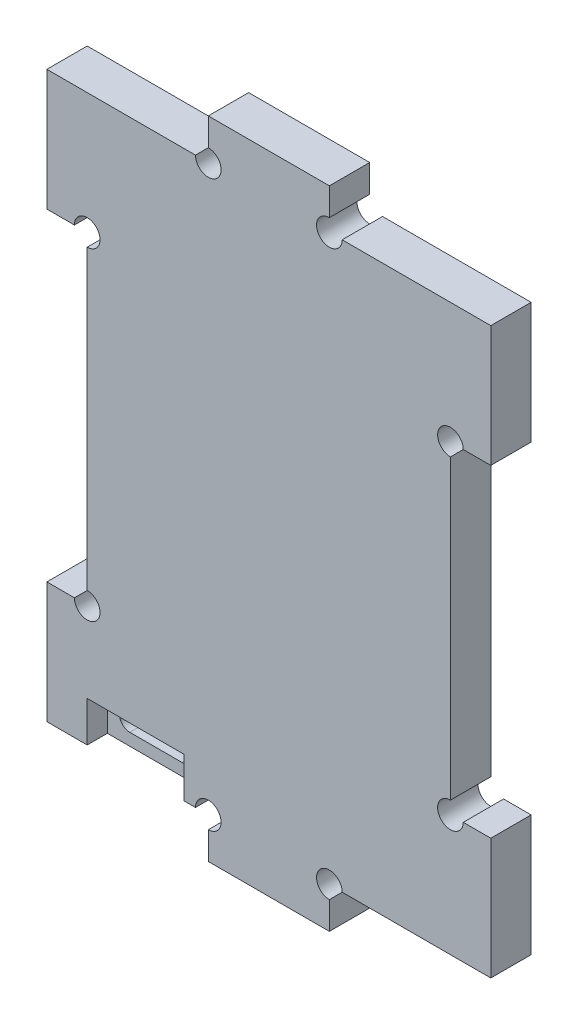
SolidWorks part; units mm, degrees
material "Acrylic (Medium-high impact)"
ref_plane "Front Plane" through (0, 0, 0) normal (0, 0, 1) x (1, 0, 0)
ref_plane "Top Plane" through (0, 0, 0) normal (0, 1, 0) x (1, 0, 0)
ref_plane "Right Plane" through (0, 0, 0) normal (1, 0, 0) x (0, 0, -1)
sketch "Sketch2" plane through (0, 0, 0) normal (0, 0, 1) x (1, 0, 0)
  line L0 (-7.5, 40) -> (7.5, 40)
  line L1 (7.5, 40) -> (7.5, 35)
  line L2 (7.5, 35) -> (27.5, 35)
  line L3 (27.5, 35) -> (27.5, -35)
  line L4 (0, 0) -> (27.5, 0) construction
  line L5 (0, -40) -> (0, 40) construction
  line L6 (-27.5, 35) -> (-27.5, -35)
  line L7 (-7.5, 35) -> (-27.5, 35)
  line L8 (-7.5, 40) -> (-7.5, 35)
  line L9 (-7.5, -40) -> (-7.5, -35)
  line L10 (-7.5, -35) -> (-27.5, -35)
  line L11 (7.5, -35) -> (27.5, -35)
  line L12 (7.5, -40) -> (7.5, -35)
  line L13 (-7.5, -40) -> (7.5, -40)
  point P17 (-27.5, 0)
  dimension "D1" = 5
  dimension "D2" = 27.5
  dimension "D3" = 7.5
  dimension "D4" = 40
extrude "Boss-Extrude2" add sketch "Sketch2" along normal blind 5
sketch "Sketch3" plane through (0, 0, 5) normal (0, 0, 1) x (1, 0, 0)
  line L0 (0, 0) -> (-27.5, 0) construction
  line L1 (-27.5, 35) -> (-27.5, -35) construction
  line L3 (-22.5, -20) -> (-27.5, -20)
  line L4 (-22.5, -20) -> (-22.5, 20)
  line L5 (-22.5, 20) -> (-27.5, 20)
  line L6 (-27.5, -20) -> (-27.5, 20)
  line L7 (-22.5, -20) -> (-27.5, 20) construction
  line L8 (-22.5, 20) -> (-27.5, -20) construction
  point P5 (-25, 0)
  point P8 (-27.5, 0)
  dimension "D1" = 40
  dimension "D2" = 5
extrude "Cut-Extrude1" cut sketch "Sketch3" against normal blind 5
mirror "Mirror1" about plane through (0, 0, 0) normal (1, 0, 0) of "Cut-Extrude1"
sketch "Sketch5" plane through (0, 0, 5) normal (0, 0, 1) x (1, 0, 0)
  line L0 (7.5, -35) -> (27.5, -35) construction
  line L1 (-10.5, -35) -> (-22.5, -35)
  line L2 (-10.5, -35) -> (-10.5, -30)
  line L3 (-10.5, -30) -> (-22.5, -30)
  line L4 (-22.5, -35) -> (-22.5, -30)
  line L5 (-10.5, -35) -> (-22.5, -30) construction
  line L6 (-10.5, -30) -> (-22.5, -35) construction
  line L8 (-22.5, -20) -> (-22.5, 20) construction
  point P0 (-16.5, -32.5)
  point P5 (18.1027, -29.1952)
  dimension "D1" = 12
  dimension "D2" = 5
extrude "Cut-Extrude2" cut sketch "Sketch5" against normal blind 2.5
sketch "Sketch6" plane through (0, 0, 2.5) normal (0, 0, 1) x (1, 0, 0)
  line L0 (-22.5, -35) -> (-10.5, -35) construction
  line L1 (-19.72, -33.5) -> (-13.28, -33.5)
  line L2 (-21, -32.22) -> (-21, -31.58)
  line L3 (-19.72, -30.3) -> (-13.28, -30.3)
  line L4 (-12, -32.22) -> (-12, -31.58)
  line L5 (-16.5, -35) -> (-16.5, -30) construction
  line L6 (-10.5, -30) -> (-22.5, -30) construction
  arc A0 (-19.72, -30.3) -> (-21, -31.58) centre (-19.72, -31.58) ccw
  arc A1 (-19.72, -33.5) -> (-21, -32.22) centre (-19.72, -32.22) cw
  arc A2 (-13.28, -30.3) -> (-12, -31.58) centre (-13.28, -31.58) cw
  arc A3 (-12, -32.22) -> (-13.28, -33.5) centre (-13.28, -32.22) cw
  point P10 (-16.5, -33.5)
  point P17 (-12, -30.3)
  point P20 (-12, -33.5)
  dimension "D4" = 1.28
  dimension "D5" = 1.28
  dimension "D6" = 1.28
  dimension "D1" = 1.5
  dimension "D2" = 9
  dimension "D3" = 3.2
extrude "Cut-Extrude3" cut sketch "Sketch6" against normal through all
sketch "Sketch7" plane through (0, 0, 5) normal (0, 0, 1) x (1, 0, 0)
  circle A0 centre (-7.5, 35) radius 1.5875
  circle A1 centre (7.5, 35) radius 1.5875
  circle A2 centre (22.5, 20) radius 1.5875
  circle A3 centre (-22.5, 20) radius 1.5875
  circle A4 centre (-22.5, -20) radius 1.5875
  circle A5 centre (-7.5, -35) radius 1.5875
  circle A6 centre (7.5, -35) radius 1.5875
  circle A7 centre (22.5, -20) radius 1.5875
  point P14 (-19.3967, -17.3509)
  point P24 (21.5505, -18.7973)
  dimension "D1" = 3.175
extrude "Cut-Extrude4" cut sketch "Sketch7" against normal through all
equation "\"cortador\"=8.65458"
